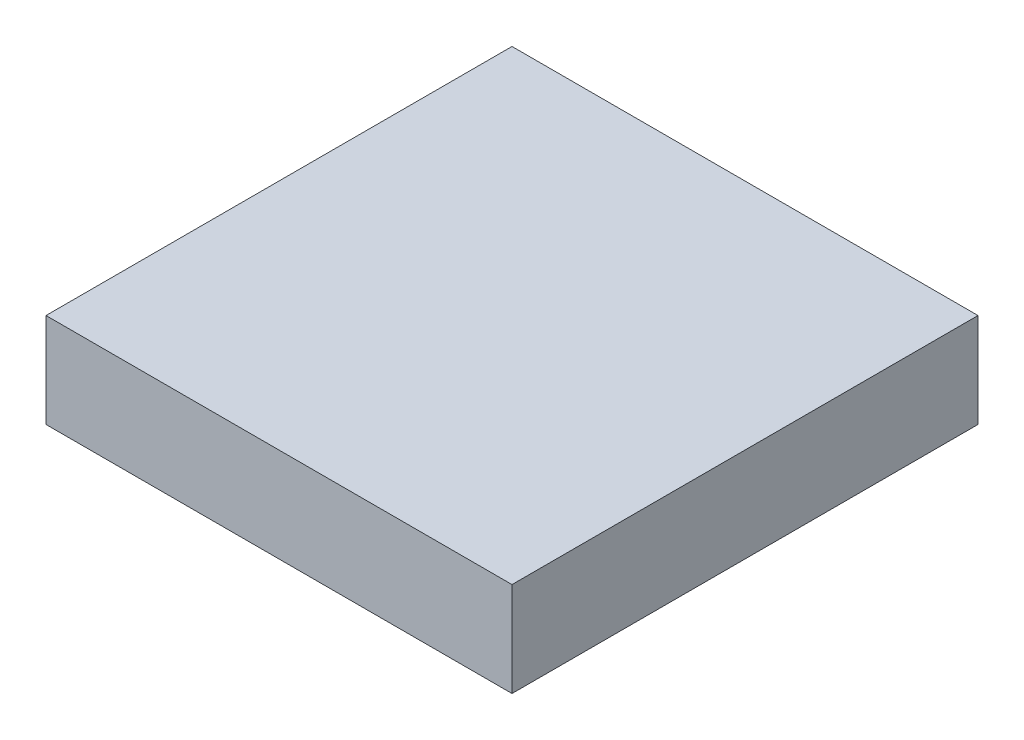
SolidWorks part; units mm, degrees
ref_plane "Front Plane" through (0, 0, 0) normal (0, 0, 1) x (1, 0, 0)
ref_plane "Top Plane" through (0, 0, 0) normal (0, 1, 0) x (1, 0, 0)
ref_plane "Right Plane" through (0, 0, 0) normal (1, 0, 0) x (0, 0, -1)
sketch "Sketch1" plane through (0, 0, 0) normal (0, 1, 0) x (1, 0, 0)
  line L1 (7.9, 7.9) -> (-7.9, 7.9)
  line L2 (7.9, 7.9) -> (7.9, -7.9)
  line L3 (7.9, -7.9) -> (-7.9, -7.9)
  line L4 (-7.9, 7.9) -> (-7.9, -7.9)
  line L5 (7.9, 7.9) -> (-7.9, -7.9) construction
  line L6 (7.9, -7.9) -> (-7.9, 7.9) construction
  point P0 (0, 0)
  dimension "D1" = 15.8
extrude "Base" add sketch "Sketch1" along normal blind 3.2
sketch "Sketch2" plane through (0, 0, 0) normal (0, -1, 0) x (1, 0, 0)
  line L0 (0, 6.7) -> (0, -6.7) construction
  line L1 (6.7, 6.7) -> (-6.7, 6.7)
  line L2 (6.7, 6.7) -> (6.7, -6.7)
  line L3 (6.7, -6.7) -> (-6.7, -6.7)
  line L4 (-6.7, 6.7) -> (-6.7, -6.7)
  line L5 (6.7, 6.7) -> (-6.7, -6.7) construction
  line L6 (6.7, -6.7) -> (-6.7, 6.7) construction
  line L7 (-6.7, 0) -> (6.7, 0) construction
  line L8 (-7.9, -7.9) -> (-7.9, 7.9) construction
  circle A4 centre (0, 0) radius 3.3
  circle A5 centre (0, 0) radius 2.5
  point P0 (0, 0)
  dimension "D4" = 5
  dimension "D2" = 1.2
  dimension "D5" = 0.8
extrude "Cut-Extrude2" cut sketch "Sketch2" against normal offset from surface (2 mm away) 1.2 contours L1 L4 L3 L2 A4 | A5 up to face at (0, 3.2, 0)
equation "\"P\"= \"LegoUnit\" * 5"
equation "\"D1@Sketch1\" = \"BrickSize\" * 2 - \"Padding\""
equation "\"Padding\"= \"LegoUnit\" / 8"
equation "\"SmallHeight\"= \"LegoUnit\" * 2"
equation "\"LargeHight\"= \"LegoUnit\" * 6"
equation "\"D1@Base\" = \"SmallHeight\""
equation "\"InsetDiameter\"= \"LegoUnit\" * 2 - \"Padding\" * 3"
equation "\"LegoUnit\"=1.6"
equation "\"BrickSize\"= \"LegoUnit\" * 5"
equation "\"WallSize\"= \"LegoUnit\" - \"Padding\" * 2"
equation "\"D2@Sketch2\"=\"WallSize\""
equation "\"BumpSize\"= \"LegoUnit\" * 3"
equation "\"InsideBumpSize\"= \"BumpSize\" + \"Padding\""
equation "\"InnerWallSize\"= \"Padding\" * 4"
equation "\"D5@Sketch2\"=\"InnerWallSize\""
equation "\"CeilingSize\"= \"LegoUnit\" - \"Padding\" * 2"
equation "\"D1@Cut-Extrude2\"=\"CeilingSize\""
equation "\"D4@Sketch2\"=\"InsideBumpSize\""
